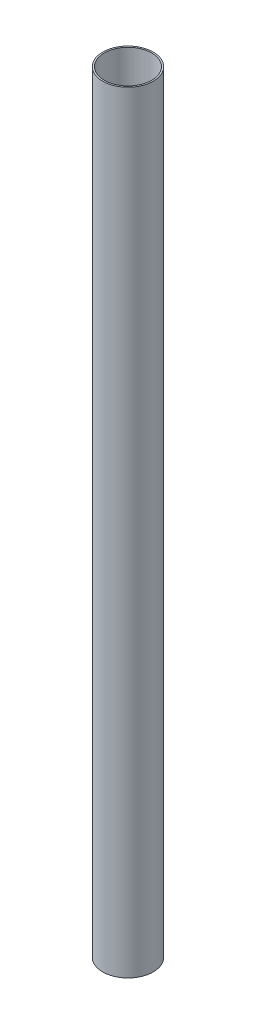
SolidWorks part; units mm, degrees
material "Hexcel AS4C (3000 Filaments)"
ref_plane "Front Plane" through (0, 0, 0) normal (0, 0, 1) x (1, 0, 0)
ref_plane "Top Plane" through (0, 0, 0) normal (0, 1, 0) x (1, 0, 0)
ref_plane "Right Plane" through (0, 0, 0) normal (1, 0, 0) x (0, 0, -1)
sketch "Sketch1" plane through (0, 0, 0) normal (0, 1, 0) x (1, 0, 0)
  circle A0 centre (0, 0) radius 27.3304
  circle A1 centre (0, 0) radius 29.1084
  dimension "D1" = 54.6608
  dimension "D2" = 1.778
extrude "Boss-Extrude1" add sketch "Sketch1" along normal up to surface (888.746 mm away)
